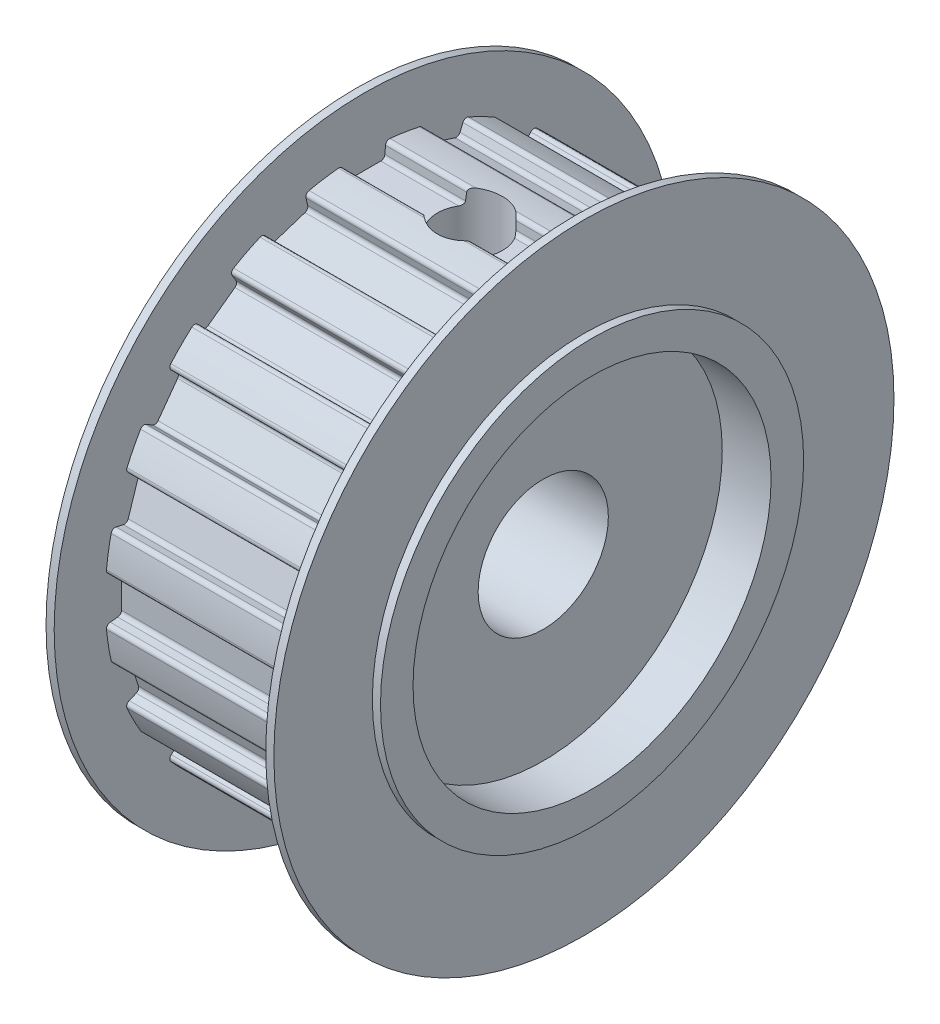
SolidWorks part; units mm, degrees
ref_plane "Plan de face" through (0, 0, 0) normal (0, 0, 1) x (1, 0, 0)
ref_plane "Plan de dessus" through (0, 0, 0) normal (0, 1, 0) x (1, 0, 0)
ref_plane "Plan de droite" through (0, 0, 0) normal (1, 0, 0) x (0, 0, -1)
sketch "Esquisse1" plane through (0, 0, 0) normal (1, 0, 0) x (0, 0, -1)
  circle A0 centre (0, 0) radius 15.915
  dimension "D1" = 31.83
extrude "Extrusion1" add sketch "Esquisse1" along normal blind 13
sketch "Esquisse22" plane through (0, 0, 0) normal (-1, 0, 0) x (0, 0, 1)
  line L0 (0, 0) -> (0, 15.915) construction
  line L1 (-1.25, 14.915) -> (1.25, 14.915)
  line L2 (0, 0) -> (1.25, 14.915) construction
  line L3 (0, 0) -> (-1.25, 14.915) construction
  line L4 (-1.25, 14.915) -> (-2.1271, 25.381)
  line L5 (1.25, 14.915) -> (2.1266, 25.3749)
  line L6 (-2.1271, 25.381) -> (2.1266, 25.3749)
  circle A0 centre (0, 0) radius 15.915 construction
  dimension "D1" = 2.5
  dimension "D2" = 1.25
  dimension "D3" = 1
  dimension "D4" = 180
  dimension "D5" = 180
extrude "Enlèv. mat.-Extru.2" cut sketch "Esquisse22" against normal up to next (13 mm away)
fillet "Congé1" radius 0.25 1 edges at (6.5, 14.915, -1.25)
fillet "Congé2" radius 0.25 1 edges at (6.5, 15.8594, -1.3291)
fillet "Congé3" radius 0.25 1 edges at (6.5, 14.915, 1.25)
fillet "Congé4" radius 0.25 1 edges at (6.5, 15.8594, 1.3291)
pattern_circular "Répétition circulaire1" count 20 over 360 about axis through (0, 0, 0) along (1, 0, 0) of "Enlèv. mat.-Extru.2", "Congé1", "Congé2", "Congé3", "Congé4"
sketch "Esquisse23" plane through (0, 0, 0) normal (-1, 0, 0) x (0, 0, 1)
  circle A0 centre (0, 0) radius 19.05
  dimension "D1" = 38.1
extrude "Extrusion2" add sketch "Esquisse23" along normal blind 1
sketch "Esquisse24" plane through (13, 0, 0) normal (1, 0, 0) x (0, 0, -1)
  circle A0 centre (0, 0) radius 19.05
  dimension "D1" = 38.1
extrude "Extrusion3" add sketch "Esquisse24" along normal blind 1
sketch "Esquisse25" plane through (-1, 0, 0) normal (-1, 0, 0) x (0, 0, 1)
  circle A0 centre (0, 0) radius 4
  dimension "D1" = 8
extrude "Enlèv. mat.-Extru.3" cut sketch "Esquisse25" against normal through all
sketch "Esquisse30" plane through (0, 14.915, 0) normal (0, 1, 0) x (-1, 0, 0)
  line L1 (-13, 0) -> (0, 0) construction
  line L3 (0, -1.0201) -> (0, 1.0201) construction
  circle A0 centre (-6.5, 0) radius 2
  dimension "D2" = 4
  dimension "D1" = 6.5
extrude "Enlèv. mat.-Extru.5" cut sketch "Esquisse30" against normal up to next and the other way through all
sketch "Esquisse31" plane through (-1, 0, 0) normal (-1, 0, 0) x (0, 0, 1)
  circle A0 centre (0, 0) radius 13
  dimension "D1" = 26
extrude "Enlèv. mat.-Extru.6" cut sketch "Esquisse31" against normal blind 0.5 flip side to cut
sketch "Esquisse32" plane through (14, 0, 0) normal (1, 0, 0) x (0, 0, -1)
  circle A0 centre (0, 0) radius 13
  dimension "D1" = 26
extrude "Enlèv. mat.-Extru.7" cut sketch "Esquisse32" against normal blind 0.5 flip side to cut
chamfer "Chanfrein1" distance 0.25 angle 45 1 edges at (14, 0, 4)
chamfer "Chanfrein2" distance 0.25 angle 45 1 edges at (-1, 0, 4)
sketch "Esquisse33" plane through (14, 0, 0) normal (1, 0, 0) x (0, 0, -1)
  circle A0 centre (0, 0) radius 11
extrude "Extrusion4" cut sketch "Esquisse33" against normal blind 3
